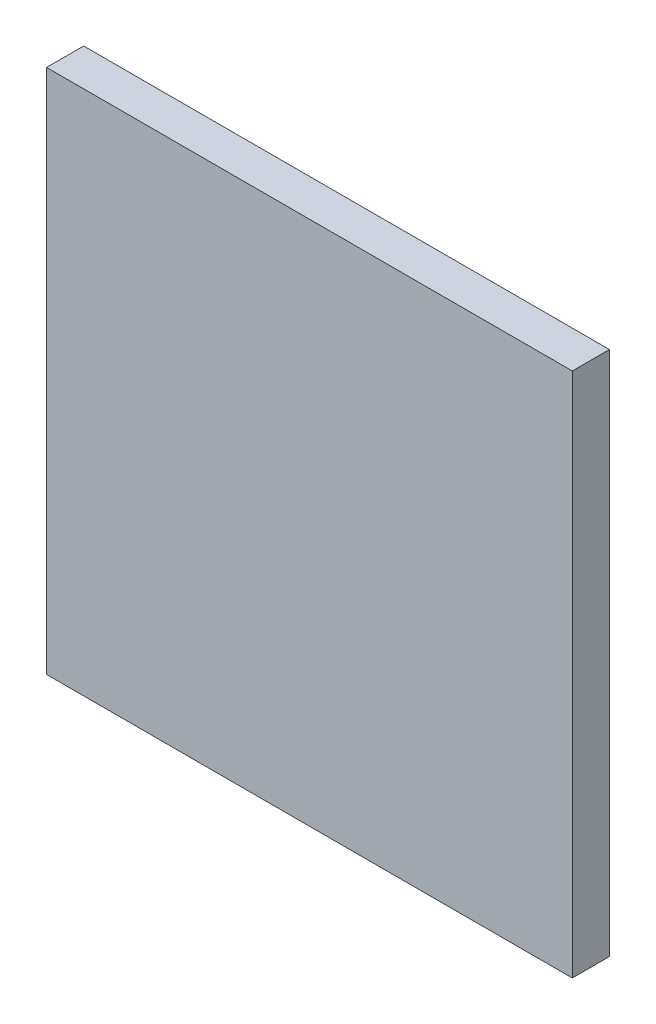
SolidWorks part; units mm, degrees
ref_plane "Front Plane" through (0, 0, 0) normal (0, 0, 1) x (1, 0, 0)
ref_plane "Top Plane" through (0, 0, 0) normal (0, 1, 0) x (1, 0, 0)
ref_plane "Right Plane" through (0, 0, 0) normal (1, 0, 0) x (0, 0, -1)
sketch "Sketch1" plane through (0, 0, 0) normal (0, 0, 1) x (1, 0, 0)
  line L1 (8.5, 8.5) -> (-8.5, 8.5)
  line L2 (8.5, 8.5) -> (8.5, -8.5)
  line L3 (8.5, -8.5) -> (-8.5, -8.5)
  line L4 (-8.5, 8.5) -> (-8.5, -8.5)
  line L5 (8.5, 8.5) -> (-8.5, -8.5) construction
  line L6 (8.5, -8.5) -> (-8.5, 8.5) construction
  point P0 (0, 0)
  dimension "D1" = 17
extrude "Boss-Extrude1" add sketch "Sketch1" along normal blind 1.2
ref_plane "Plane1" through (0, 0, 0) normal (-1, 0, 0) x (0, 0, 1)
ref_plane "Plane2" through (0, 0, 0) normal (0, -1, 0) x (-1, 0, 0)
